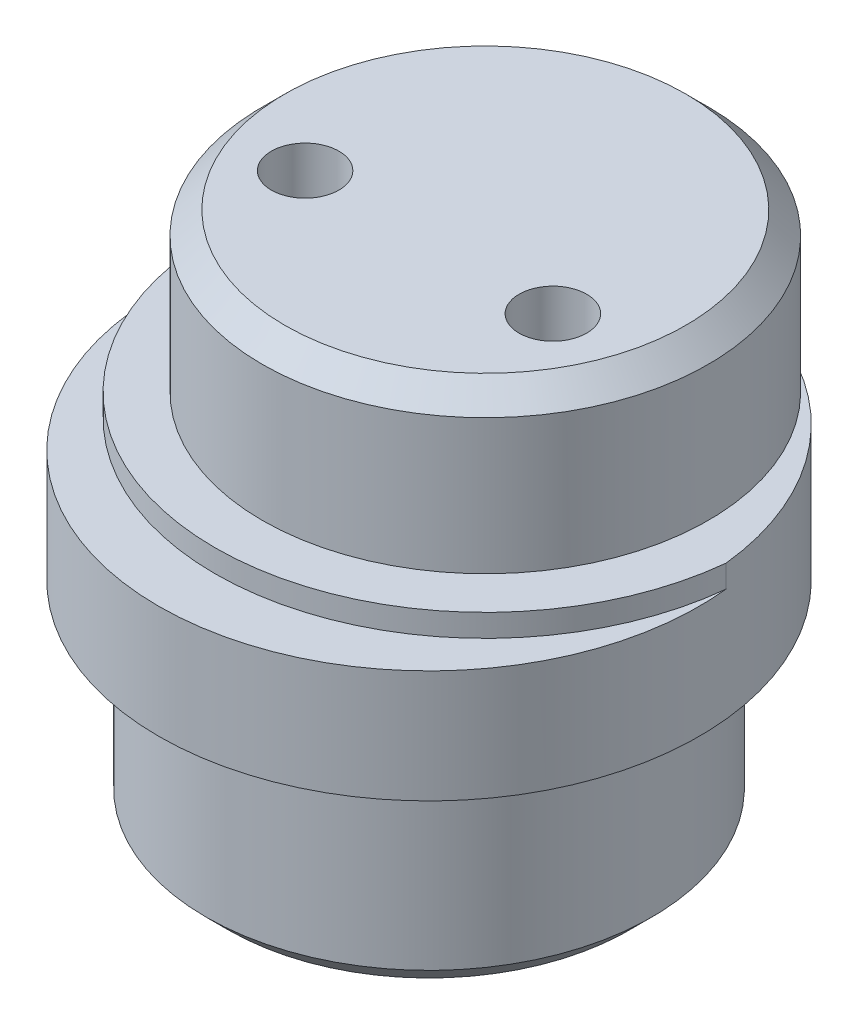
SolidWorks part; units mm, degrees
ref_plane "Front Plane" through (0, 0, 0) normal (0, 0, 1) x (1, 0, 0)
ref_plane "Top Plane" through (0, 0, 0) normal (0, 1, 0) x (1, 0, 0)
ref_plane "Right Plane" through (0, 0, 0) normal (1, 0, 0) x (0, 0, -1)
sketch "Sketch1" plane through (0, 0, 0) normal (0, 1, 0) x (1, 0, 0)
  circle A0 centre (0, 0) radius 9.9
  dimension "D1" = 19.8
extrude "Boss-Extrude1" add sketch "Sketch1" along normal blind 9
sketch "Sketch2" plane through (0, 9, 0) normal (0, 1, 0) x (1, 0, 0)
  circle A0 centre (0, 0) radius 12
  dimension "D1" = 24
extrude "Boss-Extrude2" add sketch "Sketch2" along normal blind 6
sketch "Sketch3" plane through (0, 15, 0) normal (0, 1, 0) x (1, 0, 0)
  circle A0 centre (0, 2.5) radius 9.9
  dimension "D2" = 19.8
  dimension "D1" = 2.5
extrude "Boss-Extrude3" add sketch "Sketch3" along normal blind 7
sketch "Sketch7" plane through (0, 15, 0) normal (0, 1, 0) x (1, 0, 0)
  circle A1 centre (0, 2.5) radius 12
  circle A2 centre (0, 2.5) radius 15
  dimension "D1" = 24
  dimension "D2" = 30
extrude "Cut-Extrude3" cut sketch "Sketch7" against normal blind 1
sketch "Sketch10" plane through (0, 22, 0) normal (0, 1, 0) x (1, 0, 0)
  circle A0 centre (5.5, 0) radius 1.5
  circle A1 centre (-5.5, 0) radius 1.5
  dimension "D3" = 3
  dimension "D4" = 3
  dimension "D1" = 5.5
  dimension "D2" = 5.5
extrude "Cut-Extrude4" cut sketch "Sketch10" against normal through all
sketch "Sketch12" plane through (0, 0, 0) normal (0, -1, 0) x (-1, 0, 0)
  circle A0 centre (0, 5.5) radius 1.5
  circle A1 centre (0, -5.5) radius 1.5
  dimension "D1" = 3
  dimension "D3" = 3
  dimension "D2" = 5.5
  dimension "D4" = 5.5
extrude "Cut-Extrude5" cut sketch "Sketch12" against normal blind 12
chamfer "Chamfer1" distance 1 angle 45 2 edges at (0, 0, 9.9) (0, 22, 7.4)
equation "\"e\"= 2.5"
equation "\"D1@Sketch3\"=\"e\""
